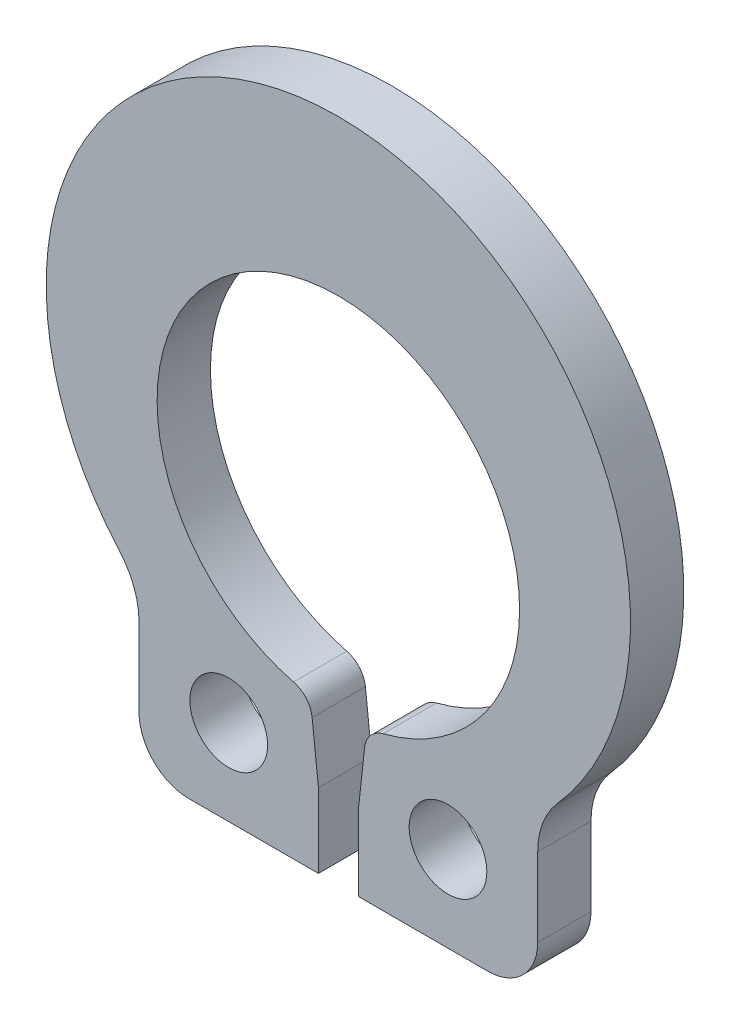
SolidWorks part; units mm, degrees
material "Alloy Steel"
ref_plane "Front Plane" through (0, 0, 0) normal (0, 0, 1) x (1, 0, 0)
ref_plane "Top Plane" through (0, 0, 0) normal (0, 1, 0) x (1, 0, 0)
ref_plane "Right Plane" through (0, 0, 0) normal (1, 0, 0) x (0, 0, -1)
sketch "Sketch1" plane through (0, 0, 0) normal (0, 0, 1) x (1, 0, 0)
  line L0 (0, 0) -> (0, -3.0226) construction
  line L1 (0, 0) -> (0, 3.0226) construction
  line L2 (0, -5.4864) -> (-3.3249, -5.4864) construction
  line L3 (0, -5.4864) -> (3.3249, -5.4864) construction
  line L4 (-3.3249, -5.4864) -> (-3.3249, -3.3464) construction
  line L5 (0, 3.0226) -> (0, 5.6134) construction
  line L6 (0, -3.0226) -> (0, -5.4864) construction
  line L7 (-1.8287, -4.058) -> (-0.3325, -4.058) construction
  line L8 (3.3249, -5.4864) -> (3.3249, -3.3464) construction
  line L9 (-1.8287, -4.058) -> (-3.3249, -4.058) construction
  line L10 (-1.8287, -4.058) -> (-1.2418, -2.7557) construction
  line L11 (-1.2418, -2.7557) -> (0, 0) construction
  line L12 (1.8287, -4.058) -> (0.3325, -4.058) construction
  line L14 (-0.3325, -5.4864) -> (-0.3325, -3.0043) construction
  line L15 (-0.3325, -3.0043) -> (0.3325, -3.0043) construction
  line L16 (0.3325, -5.4864) -> (0.3325, -3.0043) construction
  line L17 (1.8287, -4.058) -> (3.3249, -4.058) construction
  line L18 (-1.8287, -4.058) -> (-1.8287, -5.4864) construction
  circle A0 centre (0, 0) radius 3.0226 construction
  arc A1 (-3.3249, -3.3464) -> (-3.65, -2.4882) centre (-4.6203, -3.3464) ccw construction
  circle A2 centre (0, 0.7404) radius 4.873 construction
  circle A3 centre (1.8287, -4.058) radius 0.6477 construction
  circle A4 centre (-1.8287, -4.058) radius 0.6477 construction
  arc A5 (3.3249, -3.3464) -> (3.65, -2.4882) centre (4.6203, -3.3464) cw construction
  arc A6 (-3.3249, -4.6539) -> (-2.4924, -5.4864) centre (-2.4924, -4.6539) ccw construction
  arc A7 (3.3249, -4.6539) -> (2.4924, -5.4864) centre (2.4924, -4.6539) cw construction
  point P5 (0, -3.0226)
  point P20 (3.0226, 0)
  point P31 (0, -3.0043)
  point P32 (0, -4.1326)
  dimension "Ring ID" = 6.0452
  dimension "D4" = 1.2954
  dimension "Hole Dia - R" = 1.2954
  dimension "D3" = 0.8325
  dimension "Lug - H" = 2.4638
  dimension "D1" = 6.6497
  dimension "Ring Height - B" = 11.0998
  dimension "D2" = 1.11
  dimension "D5" = 0.665
sketch "Sketch2" plane through (0, 0, 0) normal (1, 0, 0) x (0, 0, -1)
  line L0 (0, 0) -> (-0.4445, 0) construction
  line L1 (0, 0) -> (0.4445, 0) construction
  line L2 (-0.4445, 0) -> (-0.4445, 5.6134) construction
  line L3 (-0.4445, 5.6134) -> (0.4445, 5.6134) construction
  line L4 (0.4445, 5.6134) -> (0.4445, 0) construction
  dimension "Ring Thickness" = 0.889
sketch "Sketch3" plane through (0, 0, 0) normal (0, 0, 1) x (1, 0, 0)
  line L0 (3.3249, -5.4864) -> (3.3249, -3.3464) construction
  line L1 (0, -5.4864) -> (3.3249, -5.4864) construction
  line L2 (0, -5.4864) -> (-3.3249, -5.4864) construction
  line L3 (-3.3249, -5.4864) -> (-3.3249, -3.3464) construction
  line L4 (3.3249, -4.6539) -> (3.3249, -3.3464)
  line L5 (0.3325, -5.4864) -> (2.4924, -5.4864)
  line L6 (-0.3325, -5.4864) -> (-2.4924, -5.4864)
  line L7 (-3.3249, -4.6539) -> (-3.3249, -3.3464)
  line L8 (0.3325, -5.4864) -> (0.3325, -3.0043) construction
  line L9 (-0.3325, -5.4864) -> (-0.3325, -3.0043) construction
  line L10 (0.3325, -5.4864) -> (0.3325, -3.0043)
  line L11 (-0.3325, -5.4864) -> (-0.3325, -3.0043)
  circle A0 centre (-1.8287, -4.058) radius 0.6477 construction
  circle A1 centre (1.8287, -4.058) radius 0.6477 construction
  arc A2 (3.65, -2.4882) -> (3.3249, -3.3464) centre (4.6203, -3.3464) ccw construction
  arc A3 (2.4924, -5.4864) -> (3.3249, -4.6539) centre (2.4924, -4.6539) ccw construction
  arc A4 (-3.3249, -4.6539) -> (-2.4924, -5.4864) centre (-2.4924, -4.6539) ccw construction
  arc A5 (-3.3249, -3.3464) -> (-3.65, -2.4882) centre (-4.6203, -3.3464) ccw construction
  circle A6 centre (0, 0) radius 3.0226 construction
  circle A8 centre (-1.8287, -4.058) radius 0.6477
  circle A9 centre (1.8287, -4.058) radius 0.6477
  arc A10 (3.65, -2.4882) -> (3.3249, -3.3464) centre (4.6203, -3.3464) ccw
  arc A11 (2.4924, -5.4864) -> (3.3249, -4.6539) centre (2.4924, -4.6539) ccw
  arc A12 (-3.3249, -4.6539) -> (-2.4924, -5.4864) centre (-2.4924, -4.6539) ccw
  arc A13 (-3.3249, -3.3464) -> (-3.65, -2.4882) centre (-4.6203, -3.3464) ccw
  arc A14 (0.3325, -3.0043) -> (-0.3325, -3.0043) centre (0, 0) ccw
  circle A16 centre (0, 0.7404) radius 4.873 construction
  arc A17 (3.65, -2.4882) -> (-3.65, -2.4882) centre (0, 0.7404) ccw
extrude "Boss-Extrude1" add sketch "Sketch3" along normal mid plane 0.889
sketch "Sketch4" plane through (0, 0, 0) normal (0, 0, 1) x (1, 0, 0)
  line L0 (-0.3325, -4.2453) -> (-0.7974, 0)
  line L1 (-0.3325, -5.4864) -> (-0.3325, -3.0043) construction
  line L2 (0.3325, -4.2453) -> (0.7974, 0)
  line L3 (0.3325, -3.0043) -> (0.3325, -5.4864) construction
  line L4 (-0.7974, 0) -> (0.7974, 0)
  line L5 (-0.3325, -4.2453) -> (0.3325, -4.2453)
  point P12 (0, 0)
  dimension "D1" = 12.5
extrude "Cut-Extrude1" cut sketch "Sketch4" against normal through all both and the other way through all
fillet "Fillet1" radius 0.4162 2 edges at (0.4704, -2.9858, 0) (-0.4704, -2.9858, 0)
equation "\"D1@Sketch1\" = \"Ring ID@Sketch1\" * 1.1"
equation "\"D4@Sketch1\"=\"Hole Dia - R@Sketch1\""
equation "\"D3@Sketch1\"=\"D2@Sketch1\"*.75"
equation "\"D1@Boss-Extrude1\" = \"Ring Thickness@Sketch2\""
equation "\"D5@Sketch1\"=\"D1@Sketch1\"*.1"
equation "\"D2@Sketch1\"=\"Ring Height - B@Sketch1\"*.1"
equation "\"D1@Fillet1\"=\"D3@Sketch1\"/2"
